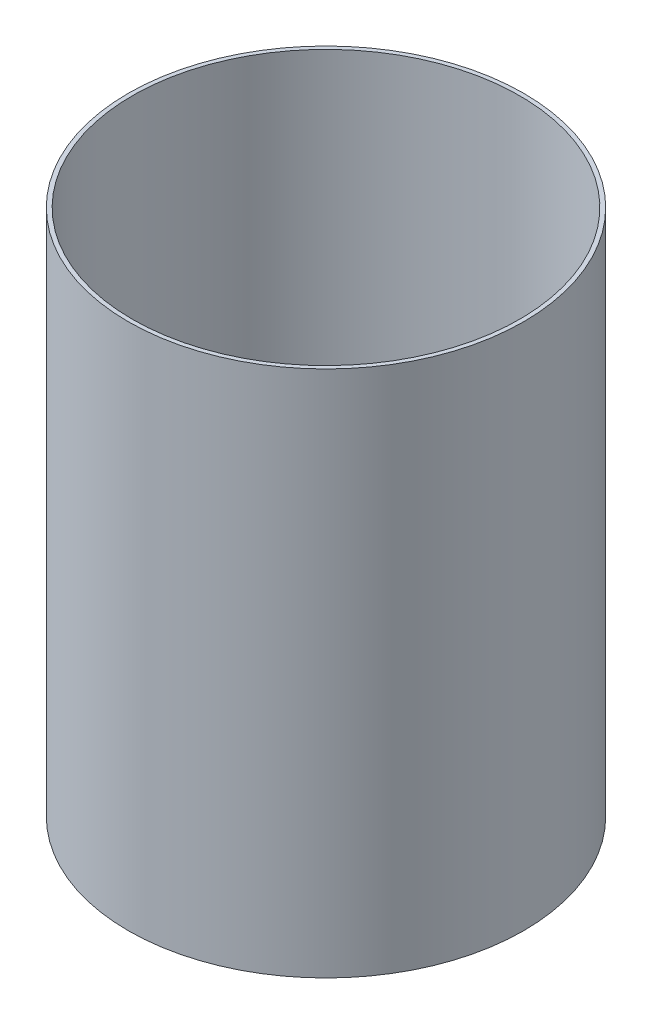
SolidWorks part; units mm, degrees
material "Hexcel AS4C (3000 Filaments)"
ref_plane "Front Plane" through (0, 0, 0) normal (0, 0, 1) x (1, 0, 0)
ref_plane "Top Plane" through (0, 0, 0) normal (0, 1, 0) x (1, 0, 0)
ref_plane "Right Plane" through (0, 0, 0) normal (1, 0, 0) x (0, 0, -1)
sketch "Sketch1" plane through (0, 0, 0) normal (0, 1, 0) x (1, 0, 0)
  circle A0 centre (0, 0) radius 149.225
  circle A1 centre (0, 0) radius 152.4
  dimension "D1" = 298.45
  dimension "D2" = 304.8
extrude "Boss-Extrude1" add sketch "Sketch1" along normal blind 406.4
